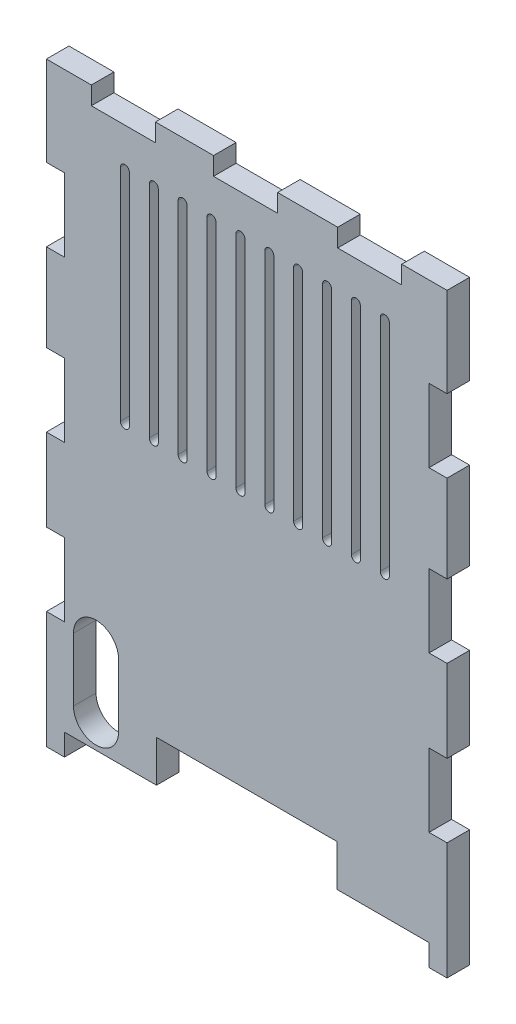
SolidWorks part; units mm, degrees
ref_plane "Plano frontal" through (0, 0, 0) normal (0, 0, 1) x (1, 0, 0)
ref_plane "Plano superior" through (0, 0, 0) normal (0, 1, 0) x (1, 0, 0)
ref_plane "Plano direito" through (0, 0, 0) normal (1, 0, 0) x (0, 0, -1)
sketch "Esboço1" plane through (0, 0, 0) normal (0, 0, 1) x (1, 0, 0)
  line L0 (-23.0984, -50.3885) -> (-25.0984, -50.3885)
  line L1 (-23.0984, 13.6153) -> (17.3016, 13.6153)
  line L2 (-23.0984, 13.6115) -> (-23.0984, -50.3885)
  line L3 (-23.0984, -50.3885) -> (17.3016, -50.3885)
  line L4 (17.3016, 13.6115) -> (17.3016, -50.3885)
  line L5 (-23.0984, -50.3885) -> (17.3016, -50.3885)
  line L6 (-23.0984, -50.3885) -> (-23.0984, -47.9885)
  line L7 (-23.0984, -47.9885) -> (17.3016, -47.9885)
  line L8 (17.3016, -50.3885) -> (17.3016, -47.9885)
  line L9 (-25.0984, 15.6115) -> (19.3016, 15.6115)
  line L10 (-25.0984, 15.6115) -> (-25.0984, -50.3885)
  line L11 (17.3016, -50.3885) -> (19.3016, -50.3885)
  line L12 (19.3016, 15.6115) -> (19.3016, -50.3885)
  line L13 (-12.8984, -47.9885) -> (7.1016, -47.9885)
  line L14 (-12.8984, -47.9885) -> (-12.8984, -50.3885)
  line L15 (-12.8984, -50.3885) -> (7.1016, -50.3885)
  line L16 (7.1016, -47.9885) -> (7.1016, -50.3885)
  line L17 (-19.5984, -37.9885) -> (-19.5984, -44.9885) construction
  line L18 (-25.0984, 5.6915) -> (-23.0984, 5.6915)
  line L19 (-25.0984, 5.6915) -> (-25.0984, -2.4085)
  line L20 (-25.0984, -2.4085) -> (-23.0984, -2.4085)
  line L21 (-23.0984, 5.6915) -> (-23.0984, -2.4085)
  line L22 (-25.0984, -12.0885) -> (-23.0984, -12.0885)
  line L23 (-25.0984, -12.0885) -> (-25.0984, -20.1885)
  line L24 (-25.0984, -20.1885) -> (-23.0984, -20.1885)
  line L25 (-23.0984, -12.0885) -> (-23.0984, -20.1885)
  line L26 (17.3016, 5.6882) -> (19.3016, 5.6882)
  line L27 (17.3016, 5.6882) -> (17.3016, -2.4118)
  line L28 (17.3016, -2.4118) -> (19.3016, -2.4118)
  line L29 (19.3016, 5.6882) -> (19.3016, -2.4118)
  line L30 (17.3016, -12.0915) -> (19.3016, -12.0915)
  line L31 (17.3016, -12.0915) -> (17.3016, -20.1915)
  line L32 (17.3016, -20.1915) -> (19.3016, -20.1915)
  line L33 (19.3016, -12.0915) -> (19.3016, -20.1915)
  line L34 (-25.0984, -29.3085) -> (-23.0984, -29.3085)
  line L35 (-25.0984, -29.3085) -> (-25.0984, -37.4085)
  line L36 (-25.0984, -37.4085) -> (-23.0984, -37.4085)
  line L37 (-23.0984, -29.3085) -> (-23.0984, -37.4085)
  line L38 (17.3016, -29.3122) -> (19.3016, -29.3122)
  line L39 (17.3016, -29.3122) -> (17.3016, -37.4122)
  line L40 (17.3016, -37.4122) -> (19.3016, -37.4122)
  line L41 (19.3016, -29.3122) -> (19.3016, -37.4122)
  line L42 (-20.1184, 15.6115) -> (-13.0184, 15.6115)
  line L43 (-20.1184, 15.6115) -> (-20.1184, 13.6153)
  line L44 (-20.1184, 13.6153) -> (-13.0184, 13.6153)
  line L45 (-13.0184, 15.6115) -> (-13.0184, 13.6153)
  line L46 (14.2816, 13.6153) -> (7.1816, 13.6153)
  line L47 (14.2816, 13.6153) -> (14.2816, 15.6115)
  line L48 (14.2816, 15.6115) -> (7.1816, 15.6115)
  line L49 (7.1816, 13.6153) -> (7.1816, 15.6115)
  line L50 (-6.5784, 15.6115) -> (0.5216, 15.6115)
  line L51 (-6.5784, 15.6115) -> (-6.5784, 13.6153)
  line L52 (-6.5784, 13.6153) -> (0.5216, 13.6153)
  line L53 (0.5216, 15.6115) -> (0.5216, 13.6153)
  line L54 (-12.8984, -47.9885) -> (7.1016, -47.9885)
  line L55 (9.7016, 9.3348) -> (9.7016, -15.0478)
  line L56 (-12.8984, -47.9885) -> (-12.8984, -43.3885)
  line L57 (-20.4982, 7.3893) -> (-20.4883, 7.3831)
  line L58 (12.9016, 9.3348) -> (12.9016, -15.0478)
  line L59 (-12.8984, -43.3885) -> (7.1016, -43.3885)
  line L60 (11.9016, 9.3348) -> (11.9016, -15.0478)
  line L61 (8.7016, 9.3348) -> (8.7016, -15.0478)
  line L62 (6.5016, 9.3348) -> (6.5016, -15.0478)
  line L63 (5.5016, 9.3348) -> (5.5016, -15.0478)
  line L64 (3.3016, 9.3348) -> (3.3016, -15.0478)
  line L65 (2.3016, 9.3348) -> (2.3016, -15.0478)
  line L66 (0.1016, 9.3348) -> (0.1016, -15.0478)
  line L67 (-0.8984, 9.3348) -> (-0.8984, -15.0478)
  line L68 (-3.0984, 9.3348) -> (-3.0984, -15.0478)
  line L69 (-4.0984, 9.3348) -> (-4.0984, -15.0478)
  line L70 (-6.2984, 9.3348) -> (-6.2984, -15.0478)
  line L71 (-7.2984, 9.3348) -> (-7.2984, -15.0478)
  line L72 (-9.4984, 9.3348) -> (-9.4984, -15.0478)
  line L73 (-10.4984, 9.3348) -> (-10.4984, -15.0478)
  line L74 (-12.6984, 9.3348) -> (-12.6984, -15.0478)
  line L75 (-13.6984, 9.3348) -> (-13.6984, -15.0478)
  line L76 (-15.8984, 9.3348) -> (-15.8984, -15.0478)
  line L77 (-16.8984, 9.3348) -> (-16.8984, -15.0478)
  line L78 (7.1016, -47.9885) -> (7.1016, -43.3885)
  line L79 (-17.0984, -37.9885) -> (-17.0984, -44.9885)
  line L80 (-22.0984, -37.9885) -> (-22.0984, -44.9885)
  arc A0 (12.9016, 9.3348) -> (11.9016, 9.3348) centre (12.4016, 9.3348) ccw
  arc A1 (-20.4982, 7.3893) -> (-20.4883, 7.3831) centre (-20.2219, 7.8247) ccw
  arc A2 (9.7016, 9.3348) -> (8.7016, 9.3348) centre (9.2016, 9.3348) ccw
  arc A3 (6.5016, 9.3348) -> (5.5016, 9.3348) centre (6.0016, 9.3348) ccw
  arc A4 (3.3016, 9.3348) -> (2.3016, 9.3348) centre (2.8016, 9.3348) ccw
  arc A5 (0.1016, 9.3348) -> (-0.8984, 9.3348) centre (-0.3984, 9.3348) ccw
  arc A6 (-3.0984, 9.3348) -> (-4.0984, 9.3348) centre (-3.5984, 9.3348) ccw
  arc A7 (-6.2984, 9.3348) -> (-7.2984, 9.3348) centre (-6.7984, 9.3348) ccw
  arc A8 (-9.4984, 9.3348) -> (-10.4984, 9.3348) centre (-9.9984, 9.3348) ccw
  arc A9 (-12.6984, 9.3348) -> (-13.6984, 9.3348) centre (-13.1984, 9.3348) ccw
  arc A10 (-15.8984, 9.3348) -> (-16.8984, 9.3348) centre (-16.3984, 9.3348) ccw
  arc A11 (12.9016, -15.0478) -> (11.9016, -15.0478) centre (12.4016, -15.0478) cw
  arc A12 (9.7016, -15.0478) -> (8.7016, -15.0478) centre (9.2016, -15.0478) cw
  arc A13 (6.5016, -15.0478) -> (5.5016, -15.0478) centre (6.0016, -15.0478) cw
  arc A14 (3.3016, -15.0478) -> (2.3016, -15.0478) centre (2.8016, -15.0478) cw
  arc A15 (0.1016, -15.0478) -> (-0.8984, -15.0478) centre (-0.3984, -15.0478) cw
  arc A16 (-3.0984, -15.0478) -> (-4.0984, -15.0478) centre (-3.5984, -15.0478) cw
  arc A17 (-6.2984, -15.0478) -> (-7.2984, -15.0478) centre (-6.7984, -15.0478) cw
  arc A18 (-9.4984, -15.0478) -> (-10.4984, -15.0478) centre (-9.9984, -15.0478) cw
  arc A19 (-12.6984, -15.0478) -> (-13.6984, -15.0478) centre (-13.1984, -15.0478) cw
  arc A20 (-15.8984, -15.0478) -> (-16.8984, -15.0478) centre (-16.3984, -15.0478) cw
  arc A21 (-17.0984, -37.9885) -> (-22.0984, -37.9885) centre (-19.5984, -37.9885) ccw
  arc A22 (-22.0984, -44.9885) -> (-17.0984, -44.9885) centre (-19.5984, -44.9885) ccw
  point P80 (8.3307, -18.1446)
  point P105 (-19.5984, -41.4885)
  point P117 (-19.5984, -47.4885)
  dimension "D5" = 10
  dimension "D6" = 10
  dimension "D7" = 10
  dimension "D8" = 7
  dimension "D20" = 9.68
  dimension "D21" = 4.98
  dimension "D22" = 6.44
  dimension "D23" = 6.66
  dimension "D11" = 1
  dimension "D2" = 64
  dimension "D3" = 44.4
  dimension "D4" = 1
  dimension "D9" = 5
  dimension "D10" = 12
  dimension "D12" = 0.5
  dimension "D13" = 12.98
  dimension "D14" = 9.12
  dimension "D15" = 2.4
  dimension "D16" = 2
  dimension "D17" = 2
  dimension "D18" = 2
  dimension "D19" = 8.1
  dimension "D24" = 20
  dimension "D25" = 8.1
  dimension "D26" = 8.1
  dimension "D27" = 8.1
  dimension "D28" = 8.1
  dimension "D29" = 8.1
  dimension "D30" = 5.02
  dimension "D31" = 7.1
  dimension "D32" = 7.1
extrude "Ressalto-extrusão1" add sketch "Esboço1" along normal blind 2.5
